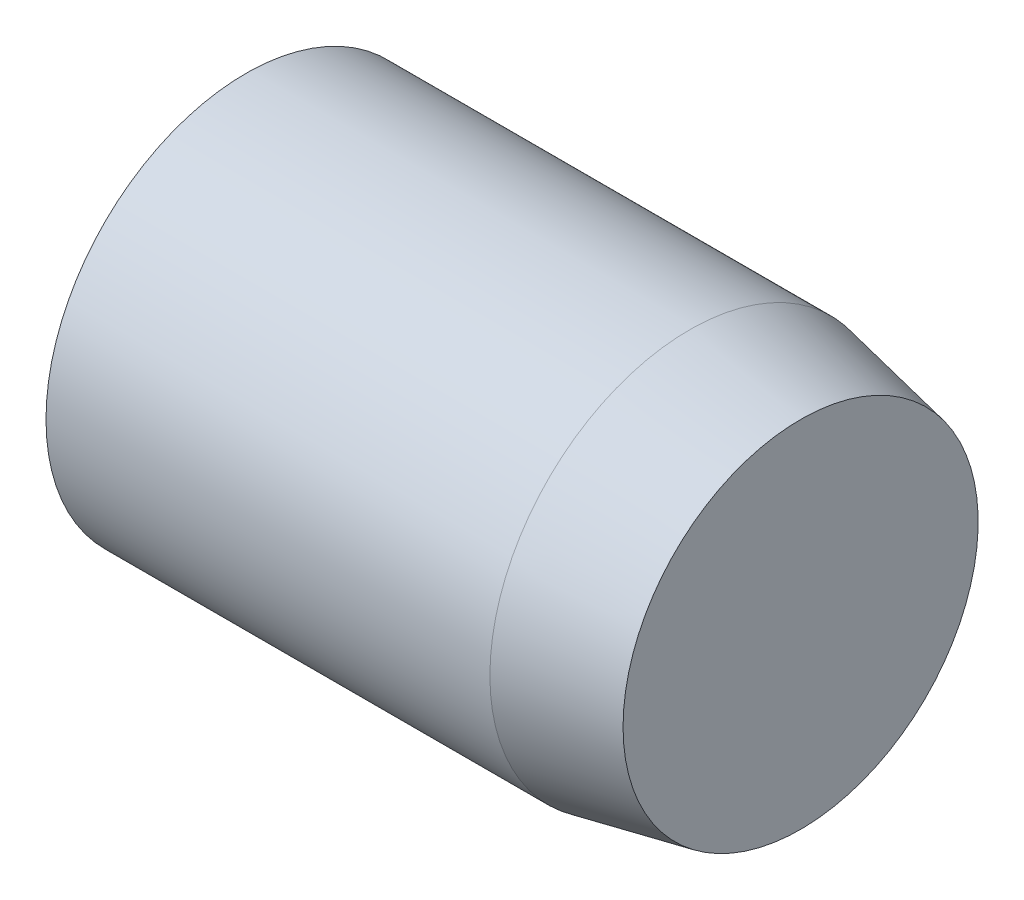
SolidWorks part; units mm, degrees
ref_plane "Front Plane" through (0, 0, 0) normal (0, 0, 1) x (1, 0, 0)
ref_plane "Top Plane" through (0, 0, 0) normal (0, 1, 0) x (1, 0, 0)
ref_plane "Right Plane" through (0, 0, 0) normal (1, 0, 0) x (0, 0, -1)
sketch "Sketch1" plane through (0, 0, 0) normal (0, 1, 0) x (1, 0, 0)
  line L0 (0, 0) -> (12.5, 0)
  line L1 (12.5, 0) -> (12.5, 4)
  line L2 (12.5, 4) -> (10, 4.5)
  line L3 (10, 4.5) -> (0, 4.5)
  line L4 (0, 4.5) -> (0, 0)
  dimension "D1" = 10
  dimension "D2" = 4.5
  dimension "D3" = 4
  dimension "D4" = 2.5
revolve "Revolve1" add sketch "Sketch1" angle 360 about L0
